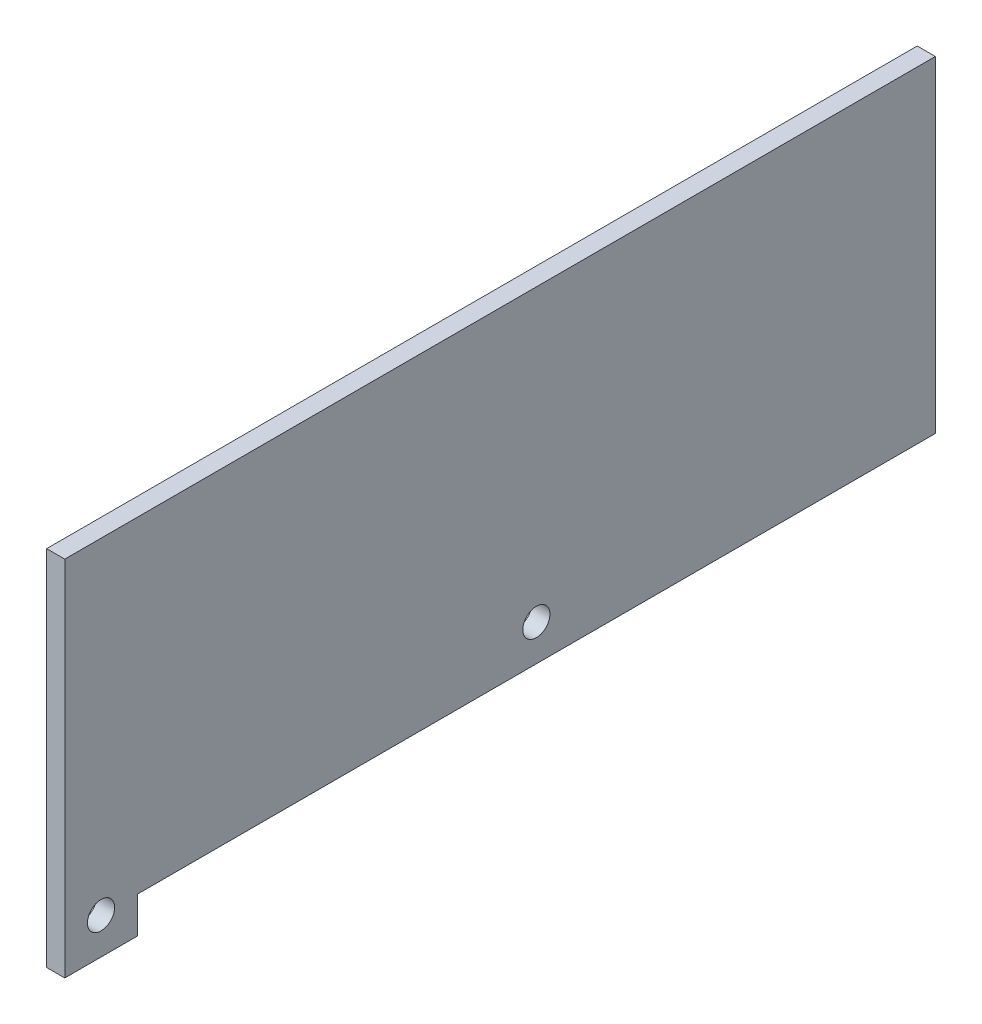
SolidWorks part; units mm, degrees
ref_plane "Front Plane" through (0, 0, 0) normal (0, 0, 1) x (1, 0, 0)
ref_plane "Top Plane" through (0, 0, 0) normal (0, 1, 0) x (1, 0, 0)
ref_plane "Right Plane" through (0, 0, 0) normal (1, 0, 0) x (0, 0, -1)
sketch "Sketch1" plane through (0, 0, 0) normal (1, 0, 0) x (0, 0, -1)
  line L0 (0, 0) -> (50.8, 0)
  line L1 (50.8, 0) -> (50.8, 25.4)
  line L2 (50.8, 25.4) -> (609.6, 25.4)
  line L3 (609.6, 25.4) -> (609.6, 254)
  line L4 (609.6, 254) -> (0, 254)
  line L5 (0, 254) -> (0, 0)
  dimension "D1" = 254
  dimension "D2" = 50.8
  dimension "D3" = 25.4
  dimension "D4" = 609.6
extrude "Boss-Extrude1" add sketch "Sketch1" along normal mid plane 12.7
sketch "Sketch2" plane through (6.35, 0, 0) normal (1, 0, 0) x (0, 0, -1)
  line L0 (0, 0) -> (50.8, 0) construction
  line L1 (0, 254) -> (0, 0) construction
  line L3 (50.8, 25.4) -> (609.6, 25.4) construction
  circle A0 centre (25.4, 25.4) radius 9.525
  circle A1 centre (330.2, 50.8) radius 9.525
  dimension "D1" = 19.05
  dimension "D2" = 25.4
  dimension "D3" = 25.4
  dimension "D4" = 304.8
  dimension "D5" = 25.4
  dimension "D6" = 19.05
extrude "Cut-Extrude1" cut sketch "Sketch2" against normal up to next
